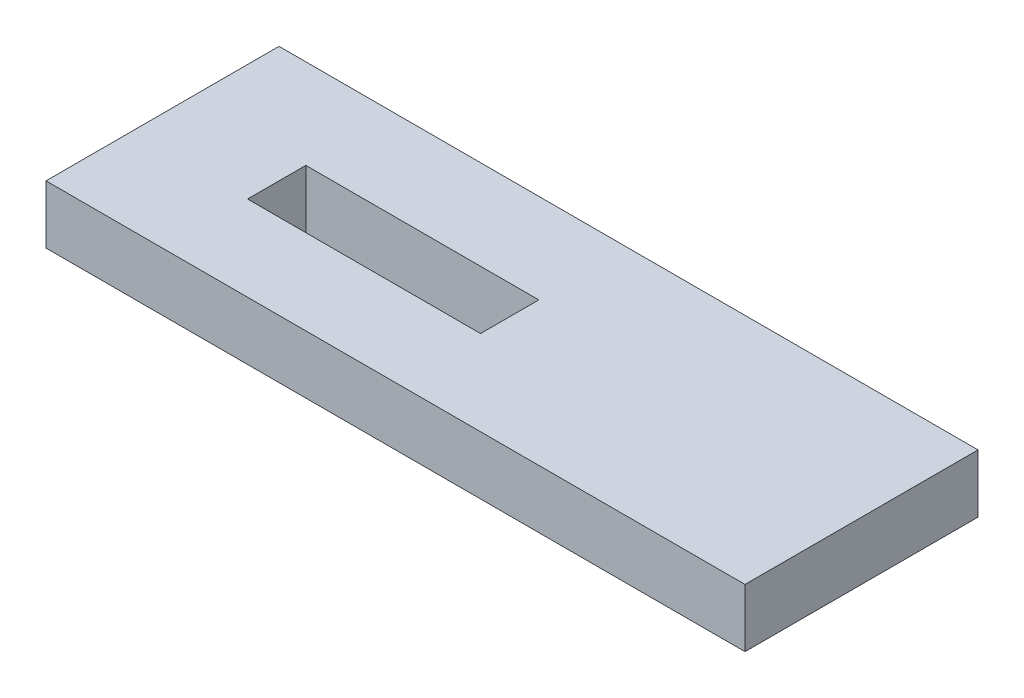
SolidWorks part; units mm, degrees
ref_plane "Front Plane" through (0, 0, 0) normal (0, 0, 1) x (1, 0, 0)
ref_plane "Top Plane" through (0, 0, 0) normal (0, 1, 0) x (1, 0, 0)
ref_plane "Right Plane" through (0, 0, 0) normal (1, 0, 0) x (0, 0, -1)
sketch "Sketch1" plane through (0, 0, 0) normal (0, 1, 0) x (1, 0, 0)
  line L1 (0, 0) -> (76.2, 0)
  line L2 (0, 0) -> (0, 25.4)
  line L3 (0, 25.4) -> (76.2, 25.4)
  line L4 (76.2, 0) -> (76.2, 25.4)
  line L5 (12.7, 15.621) -> (38.1, 15.621)
  line L6 (12.7, 15.621) -> (12.7, 9.271)
  line L7 (12.7, 9.271) -> (38.1, 9.271)
  line L8 (38.1, 15.621) -> (38.1, 9.271)
  dimension "D1" = 25.4
  dimension "D2" = 76.2
  dimension "D3" = 6.35
  dimension "D4" = 25.4
  dimension "D5" = 9.779
  dimension "D6" = 12.7
extrude "Boss-Extrude1" add sketch "Sketch1" along normal blind 6.35
